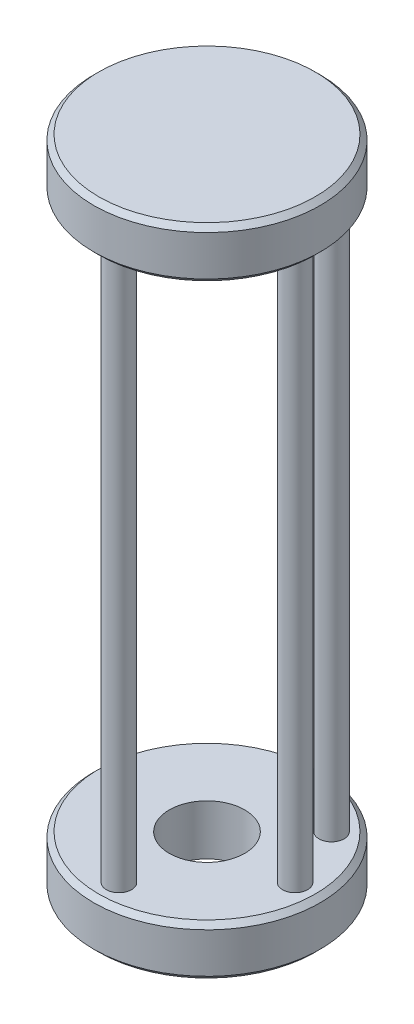
SolidWorks part; units mm, degrees
ref_plane "Front Plane" through (0, 0, 0) normal (0, 0, 1) x (1, 0, 0)
ref_plane "Top Plane" through (0, 0, 0) normal (0, 1, 0) x (1, 0, 0)
ref_plane "Right Plane" through (0, 0, 0) normal (1, 0, 0) x (0, 0, -1)
sketch "Sketch1" plane through (0, 0, 0) normal (0, 1, 0) x (1, 0, 0)
  circle A0 centre (0, 0) radius 45
  dimension "D1" = 90
extrude "Boss-Extrude1" add sketch "Sketch1" along normal blind 20
sketch "Sketch2" plane through (0, 20, 0) normal (0, 1, 0) x (1, 0, 0)
  circle A0 centre (0, 0) radius 15
  dimension "D1" = 30
extrude "Cut-Extrude1" cut sketch "Sketch2" against normal through all
sketch "Sketch3" plane through (0, 20, 0) normal (0, 1, 0) x (1, 0, 0)
  circle A0 centre (35, 0) radius 5
  circle A1 centre (0, -35) radius 5
  circle A2 centre (-35, 0) radius 5
  circle A3 centre (0, 35) radius 5
  circle A5 centre (24.7487, 24.7487) radius 5
  point P12 (0, 0)
  dimension "D1" = 10
  dimension "D4" = 10
  dimension "D2" = 35
  dimension "D5" = 35
  dimension "D6" = 45
  dimension "D3" = 4
extrude "Boss-Extrude2" add sketch "Sketch3" along normal blind 220
sketch "Sketch4" plane through (0, 240, 0) normal (0, 1, 0) x (1, 0, 0)
  circle A0 centre (0, 0) radius 45
extrude "Boss-Extrude3" add sketch "Sketch4" along normal blind 20
chamfer "Chamfer1" distance 2 angle 45 4 edges at (0, 0, 45) (0, 20, 45) (0, 240, 45) (0, 260, 45)
